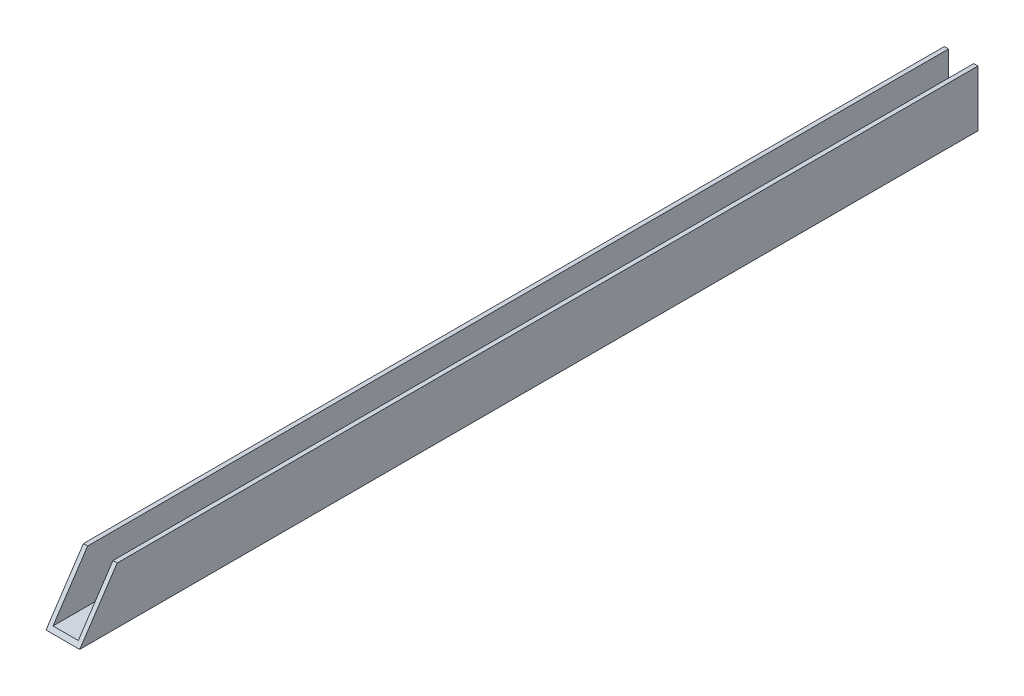
SolidWorks part; units mm, degrees
ref_plane "Front" through (0, 0, 0) normal (0, 0, 1) x (1, 0, 0)
ref_plane "Top" through (0, 0, 0) normal (0, 1, 0) x (1, 0, 0)
ref_plane "Right" through (0, 0, 0) normal (1, 0, 0) x (0, 0, -1)
sketch "Sketch1" plane through (0, 0, 0) normal (0, 0, 1) x (1, 0, 0)
  line L0 (-3.5719, 15.875) -> (-4.7625, 15.875)
  line L1 (-4.7625, 15.875) -> (-4.7625, 0)
  line L2 (-4.7625, 0) -> (4.7625, 0)
  line L3 (4.7625, 0) -> (4.7625, 15.875)
  line L4 (4.7625, 15.875) -> (3.5719, 15.875)
  line L5 (3.5719, 15.875) -> (3.5719, 1.1906)
  line L6 (3.5719, 1.1906) -> (-3.5719, 1.1906)
  line L7 (-3.5719, 1.1906) -> (-3.5719, 15.875)
  dimension "Leg THickness" = 1.1906
  dimension "BaseThickness" = 1.1906
  dimension "LegLength" = 15.875
  dimension "BaseWidth" = 9.525
extrude "Boss-Extrude1" add sketch "Sketch1" along normal mid plane 254
sketch "Sketch3" plane through (-4.7625, 0, 0) normal (-1, 0, 0) x (0, 0, 1)
  line L0 (127, 0) -> (117.6103, 14.0845)
  line L1 (117.6103, 14.0845) -> (106.1707, 31.2439)
  line L2 (106.1707, 31.2439) -> (157.6831, 12.342)
  line L3 (157.6831, 12.342) -> (127, 0)
extrude "Cut-Extrude1" cut sketch "Sketch3" against normal through all
